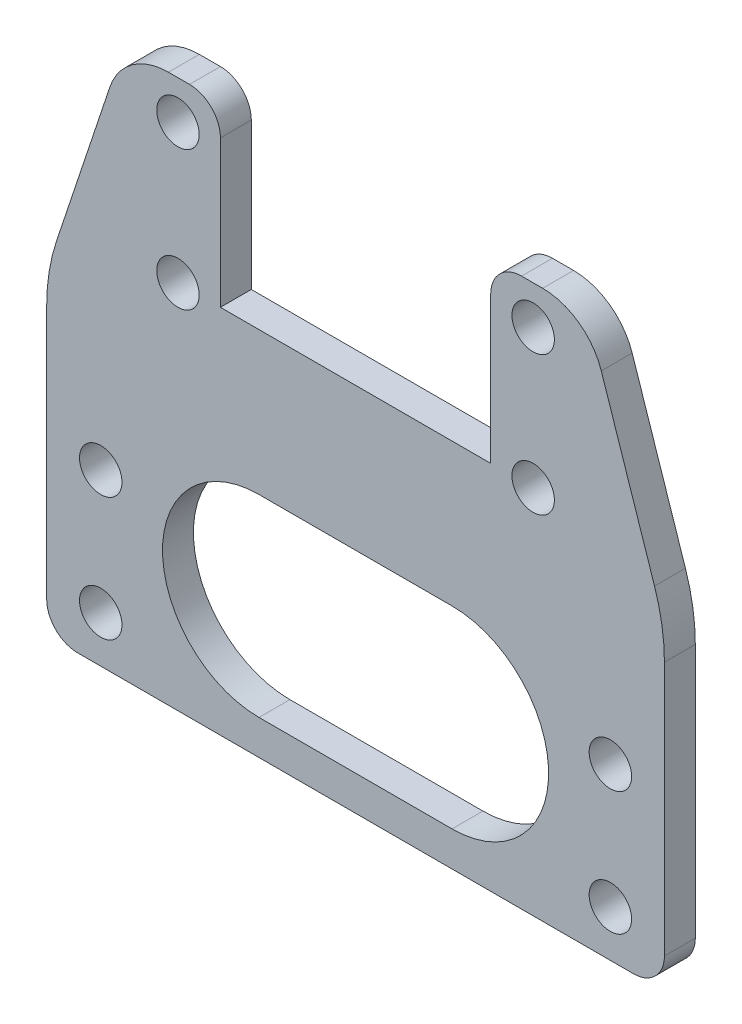
SolidWorks part; units mm, degrees
ref_plane "Спереди" through (0, 0, 0) normal (0, 0, 1) x (1, 0, 0)
ref_plane "Сверху" through (0, 0, 0) normal (0, 1, 0) x (1, 0, 0)
ref_plane "Справа" through (0, 0, 0) normal (1, 0, 0) x (0, 0, -1)
sketch "Эскиз1" plane through (0, 0, 0) normal (0, 0, 1) x (1, 0, 0)
  line L0 (18, 0) -> (-18, 0)
  line L1 (-18, 0) -> (-18, 23)
  line L2 (-18, 23) -> (-30, 23)
  line L3 (-30, 23) -> (-30, -7)
  line L4 (-40, -32) -> (40, -32)
  line L5 (0, 0) -> (0, -32) construction
  line L6 (-30, -7) -> (-40, -7)
  line L7 (-40, -7) -> (-40, -32)
  line L8 (40, -7) -> (40, -32)
  line L9 (30, -7) -> (40, -7)
  line L10 (30, 23) -> (30, -7)
  line L11 (18, 23) -> (30, 23)
  line L12 (18, 0) -> (18, 23)
  circle A0 centre (-23, 18) radius 2.75
  circle A1 centre (-23, 0) radius 2.75
  circle A2 centre (-33, -26) radius 2.75
  circle A3 centre (0, -26) radius 2.75
  circle A4 centre (33, -26) radius 2.75
  circle A5 centre (23, 18) radius 2.75
  circle A6 centre (23, 0) radius 2.75
  dimension "D2" = 18
  dimension "D3" = 25
  dimension "D7" = 6
  dimension "D8" = 33
  dimension "D9" = 5.5
  dimension "D1" = 7
  dimension "D4" = 55
  dimension "D5" = 12
  dimension "D6" = 7
  dimension "D10" = 60
  dimension "D11" = 80
  dimension "D12" = 7
extrude "Бобышка-Вытянуть1" add sketch "Эскиз1" along normal blind 4
fillet "Скругление1" [suppressed] radius 2
sketch "Эскиз2" plane through (0, 0, 0) normal (0, 0, 1) x (1, 0, 0)
  line L0 (17.5, 0) -> (-17.5, 0)
  line L1 (-17.5, 0) -> (-17.5, 23)
  line L2 (-17.5, 23) -> (-30, 23)
  line L3 (-30, 23) -> (-30, -7) construction
  line L4 (-40, -32) -> (40, -32) construction
  line L5 (0, 0) -> (0, -32) construction
  line L6 (-30, -7) -> (-40, -7) construction
  line L7 (-40, -7) -> (-40, -32)
  line L8 (40, -7) -> (40, -32)
  line L9 (30, -7) -> (40, -7) construction
  line L10 (30, 23) -> (30, -7) construction
  line L11 (17.5, 23) -> (30, 23)
  line L12 (17.5, 0) -> (17.5, 23)
  line L13 (-40, -32) -> (-40, -48)
  line L14 (-40, -48) -> (40, -48)
  line L15 (40, -48) -> (40, -32)
  line L16 (-30, 23) -> (-40, -7)
  line L17 (30, 23) -> (40, -7)
  circle A0 centre (-23, 18) radius 2.75
  circle A1 centre (-23, 0) radius 2.75
  circle A2 centre (-33, -26) radius 2.75
  circle A3 centre (-33, -42) radius 2.75
  circle A4 centre (33, -26) radius 2.75
  circle A5 centre (23, 18) radius 2.75
  circle A6 centre (23, 0) radius 2.75
  circle A7 centre (33, -42) radius 2.75
  dimension "D2" = 18
  dimension "D3" = 25
  dimension "D7" = 6
  dimension "D8" = 5.5
  dimension "D9" = 5.5
  dimension "D1" = 7
  dimension "D4" = 55
  dimension "D5" = 12.5
  dimension "D6" = 7
  dimension "D10" = 60
  dimension "D11" = 80
  dimension "D12" = 7
  dimension "D13" = 33
  dimension "D14" = 16
  dimension "D15" = 16
extrude "Бобышка-Вытянуть2" add sketch "Эскиз2" along normal blind 4
fillet "Скругление2" radius 4 4 edges at (40, -48, 2) (-40, -48, 2) (17.5, 23, 2) (-17.5, 23, 2)
fillet "Скругление3" radius 8 2 edges at (30, 23, 2) (-30, 23, 2)
fillet "Скругление4" radius 25 2 edges at (40, -7, 2) (-40, -7, 2)
sketch "Эскиз3" plane through (0, 0, 4) normal (0, 0, 1) x (1, 0, 0)
  line L0 (-12.5, -31) -> (12.5, -31) construction
  line L1 (-12.5, -18.5) -> (12.5, -18.5)
  line L2 (-12.5, -43.5) -> (12.5, -43.5)
  arc A0 (-12.5, -18.5) -> (-12.5, -43.5) centre (-12.5, -31) ccw
  arc A1 (12.5, -43.5) -> (12.5, -18.5) centre (12.5, -31) ccw
  circle A2 centre (33, -26) radius 2.75 construction
  point P2 (0, -31)
  point P7 (0, 0)
  point P8 (0, -31.71)
  dimension "D3" = 5
  dimension "D1" = 25
  dimension "D2" = 25
extrude "Вырез-Вытянуть1" cut sketch "Эскиз3" against normal through all
